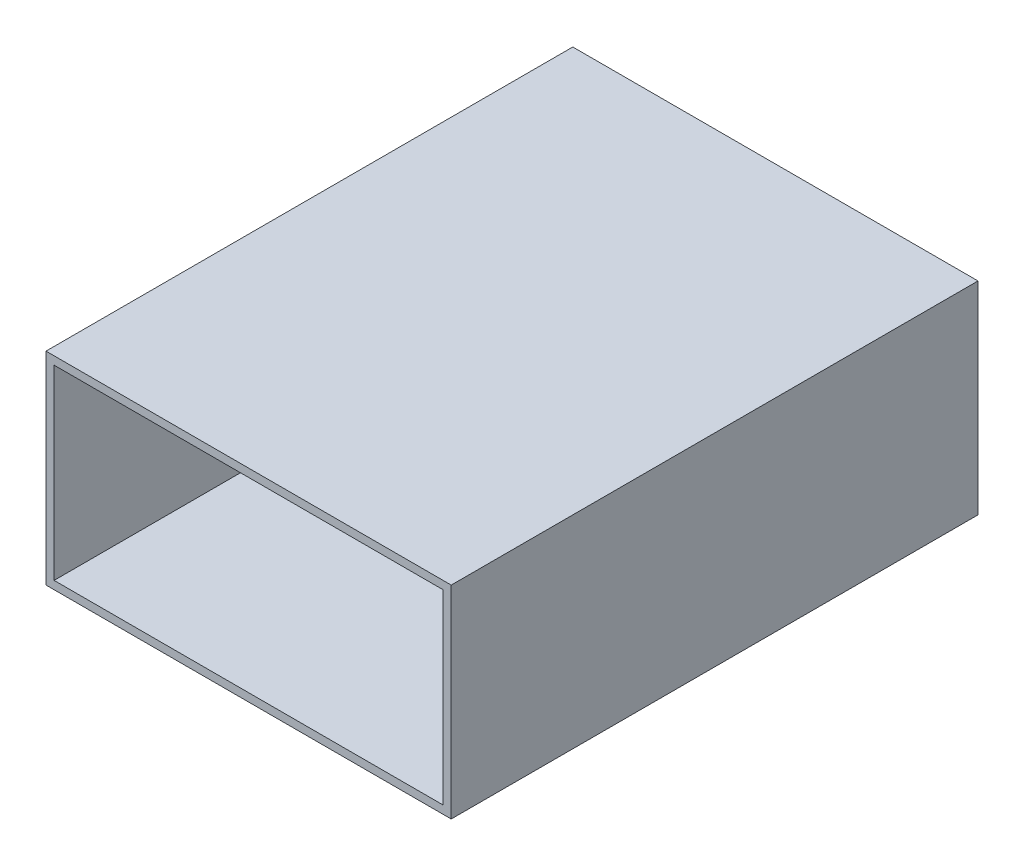
SolidWorks part; units mm, degrees
material "Stainless Steel (ferritic)"
ref_plane "Front Plane" through (0, 0, 0) normal (0, 0, 1) x (1, 0, 0)
ref_plane "Top Plane" through (0, 0, 0) normal (0, 1, 0) x (1, 0, 0)
ref_plane "Right Plane" through (0, 0, 0) normal (1, 0, 0) x (0, 0, -1)
sketch "Sketch1" plane through (0, 0, 0) normal (0, 0, 1) x (1, 0, 0)
  line L0 (-24, 11.5) -> (24, 11.5)
  line L1 (-25, -12.5) -> (25, -12.5)
  line L2 (-25, -12.5) -> (-25, 12.5)
  line L3 (-25, 12.5) -> (25, 12.5)
  line L4 (25, -12.5) -> (25, 12.5)
  line L5 (-25, -12.5) -> (25, 12.5) construction
  line L6 (-25, 12.5) -> (25, -12.5) construction
  line L7 (24, -11.5) -> (24, 11.5)
  line L8 (-24, -11.5) -> (24, -11.5)
  line L9 (-24, -11.5) -> (-24, 11.5)
  point P0 (0, 0)
  dimension "D1" = 50
  dimension "D2" = 25
  dimension "D3" = 1
extrude "Boss-Extrude1" add sketch "Sketch1" along normal blind 65
sketch "Sketch2" plane through (0, -12.5, 0) normal (0, -1, 0) x (1, 0, 0)
  line L0 (25, 65) -> (25, 0) construction
  line L1 (-25, 0) -> (25, 0) construction
  circle A0 centre (0, 20) radius 4
  dimension "D1" = 8
  dimension "D2" = 25
  dimension "D3" = 20
